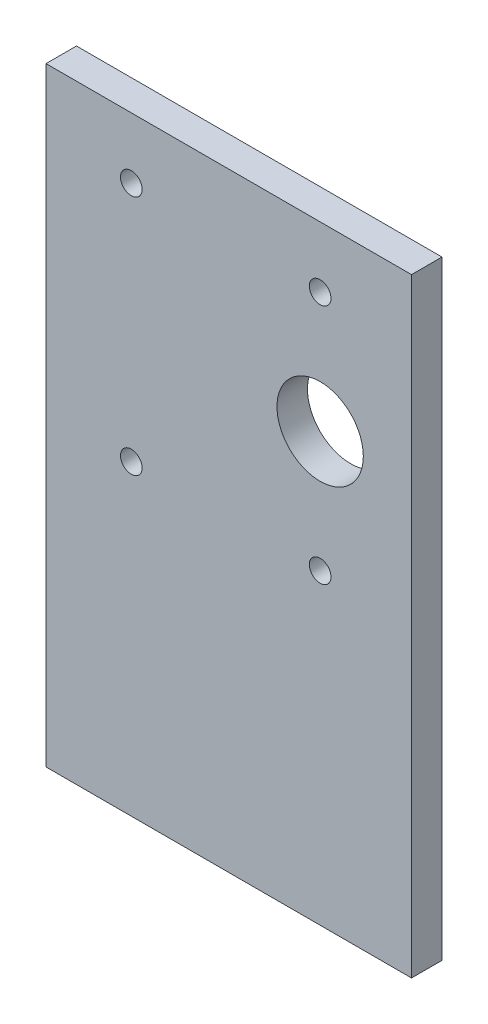
SolidWorks part; units mm, degrees
ref_plane "Front Plane" through (0, 0, 0) normal (0, 0, 1) x (1, 0, 0)
ref_plane "Top Plane" through (0, 0, 0) normal (0, 1, 0) x (1, 0, 0)
ref_plane "Right Plane" through (0, 0, 0) normal (1, 0, 0) x (0, 0, -1)
sketch "Sketch1" plane through (0, 0, 0) normal (0, 0, 1) x (1, 0, 0)
  line L1 (0, 0) -> (38.1, 0)
  line L2 (0, 0) -> (0, 63.5)
  line L3 (0, 63.5) -> (38.1, 63.5)
  line L4 (38.1, 0) -> (38.1, 63.5)
  dimension "D1" = 63.5
  dimension "D2" = 38.1
extrude "Boss-Extrude1" add sketch "Sketch1" along normal blind 3.175
sketch "Sketch3" plane through (0, 0, 3.175) normal (0, 0, 1) x (1, 0, 0)
  line L0 (38.1, 0) -> (38.1, 63.5) construction
  line L1 (28.575, 57.15) -> (8.89, 57.15)
  line L2 (28.575, 57.15) -> (28.575, 32.004)
  line L3 (28.575, 32.004) -> (8.89, 32.004)
  line L4 (8.89, 57.15) -> (8.89, 32.004)
  line L5 (38.1, 63.5) -> (0, 63.5) construction
  circle A0 centre (28.575, 44.577) radius 4.5
  point P8 (28.575, 44.577)
  dimension "D6" = 9
  dimension "D1" = 19.685
  dimension "D2" = 25.146
  dimension "D3" = 9.525
  dimension "D4" = 6.35
  dimension "D5" = 12.573
hole_wizard "#4-40 Tapped Hole1" positions "3DSketch1" profile "Sketch4" tap size "#4-40" standard "ANSI Inch" end condition through all
sketch3d "3DSketch1"
  point P0 (28.575, 57.15, 3.175)
  point P3 (28.575, 32.004, 3.175)
  point P6 (8.89, 32.004, 3.175)
  point P9 (8.89, 57.15, 3.175)
sketch "Sketch4" plane through (28.575, 57.15, 3.175) normal (1, 0, 0) x (0, -1, 0)
  line L0 (0, 0) -> (0, 3.175)
  line L1 (0, 3.175) -> (1.1303, 3.175)
  line L2 (1.1303, 3.175) -> (1.1303, 0)
  line L5 (1.1303, 0) -> (0, 0)
  line L11 (0, -6.35) -> (0, 107.95) construction
  dimension "Thru Tap Drill Dia." = 2.2606
  dimension "Thru Tap Drill Depth" = 3.175
cosmetic thread "Hole Thread1"
cosmetic thread "Hole Thread2"
cosmetic thread "Hole Thread3"
cosmetic thread "Hole Thread4"
extrude "M8 clearance hole" cut sketch "Sketch3" against normal blind 3.175 contours A0
